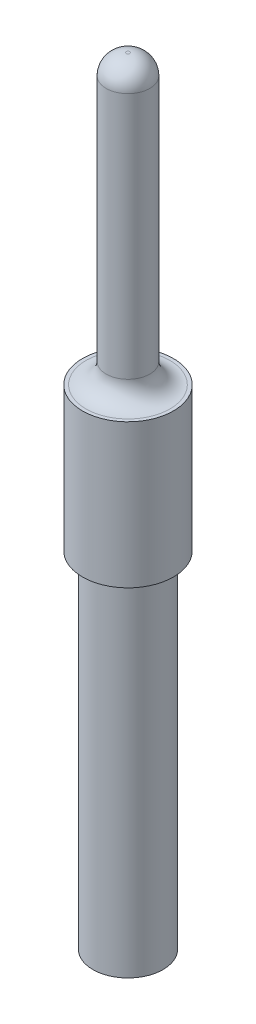
SolidWorks part; units mm, degrees
ref_plane "Front Plane" through (0, 0, 0) normal (0, 0, 1) x (1, 0, 0)
ref_plane "Top Plane" through (0, 0, 0) normal (0, 1, 0) x (1, 0, 0)
ref_plane "Right Plane" through (0, 0, 0) normal (1, 0, 0) x (0, 0, -1)
sketch "Sketch1" plane through (0, 0, 0) normal (0, 1, 0) x (1, 0, 0)
  circle A0 centre (0, 0) radius 0.61
  circle A1 centre (0, 0) radius 0.5
  dimension "D1" = 1.22
  dimension "D2" = 1
extrude "Boss-Extrude1" add sketch "Sketch1" along normal blind 6
sketch "Sketch2" plane through (0, 6, 0) normal (0, 1, 0) x (1, 0, 0)
  circle A0 centre (0, 0) radius 0.79
  dimension "D1" = 1.58
extrude "Boss-Extrude2" add sketch "Sketch2" along normal blind 2.5
sketch "Sketch3" plane through (0, 8.5, 0) normal (0, 1, 0) x (1, 0, 0)
  circle A0 centre (0, 0) radius 0.38
  dimension "D1" = 0.76
extrude "Boss-Extrude3" add sketch "Sketch3" along normal blind 5
fillet "Fillet1" radius 0.35 1 edges at (0, 13.5, 0.38)
fillet "Fillet2" radius 0.35 1 edges at (0, 8.5, 0.38)
